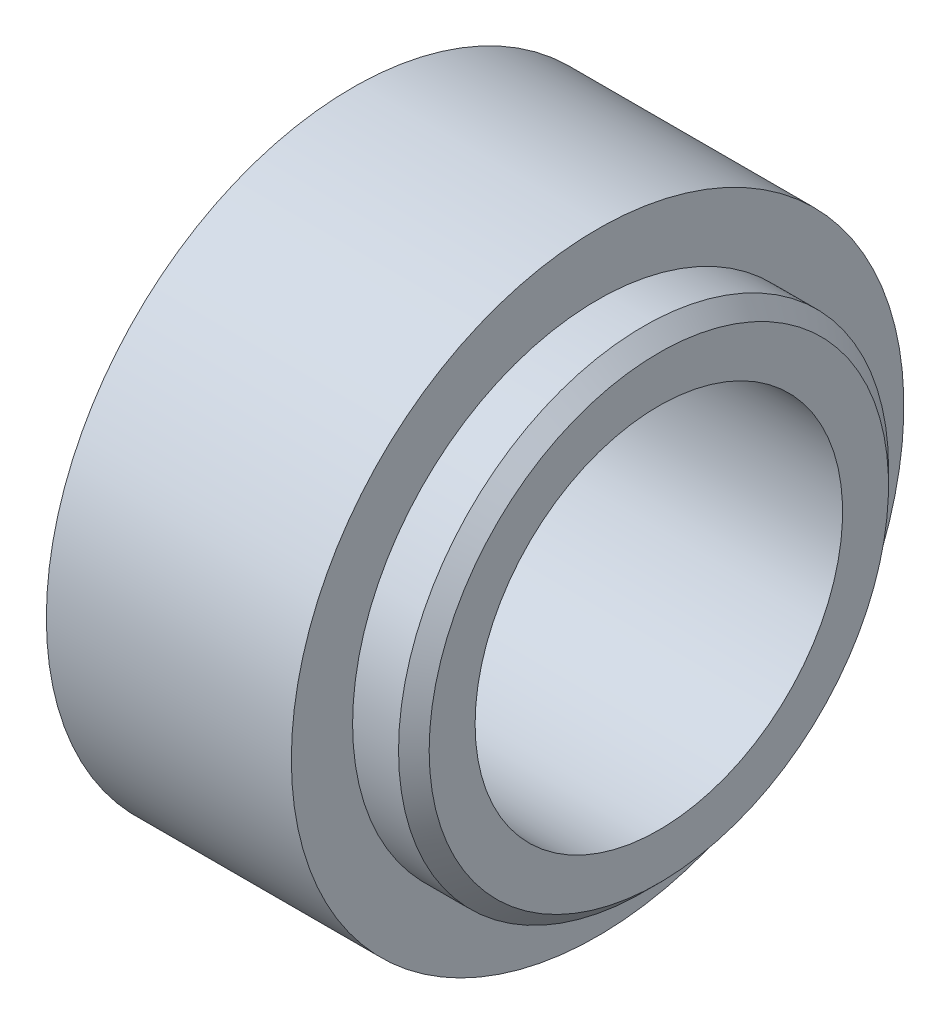
SolidWorks part; units mm, degrees
material "Tin Bearing Bronze"
ref_plane "Front Plane" through (0, 0, 0) normal (0, 0, 1) x (1, 0, 0)
ref_plane "Top Plane" through (0, 0, 0) normal (0, 1, 0) x (1, 0, 0)
ref_plane "Right Plane" through (0, 0, 0) normal (1, 0, 0) x (0, 0, -1)
sketch "Sketch1" plane through (0, 0, 0) normal (0, 0, 1) x (1, 0, 0)
  line L0 (-20.6375, 0) -> (34.2034, 0) construction
  line L1 (9.092, 19.05) -> (20.3489, 19.05)
  line L3 (20.3489, 19.05) -> (20.3489, 23.8125)
  line L5 (18.7614, 25.4) -> (13.9989, 25.4)
  line L7 (13.9989, 25.4) -> (13.9989, 31.75)
  line L9 (13.9989, 31.75) -> (-11.4011, 31.75)
  line L11 (-11.4011, 31.75) -> (-11.4011, 20.6375)
  line L13 (-11.4011, 20.6375) -> (-9.8136, 19.05)
  line L15 (-9.8136, 19.05) -> (9.092, 19.05)
  line L17 (20.3489, 23.8125) -> (18.7614, 25.4)
  point P7 (20.3489, 25.4)
  dimension "D1" = 1.5875
  dimension "D2" = 6.35
  dimension "D3" = 45
  dimension "D4" = 6.35
  dimension "D6" = 1.5875
  dimension "D7" = 45
revolve "Revolve1" add sketch "Sketch1" angle 360 about L0
